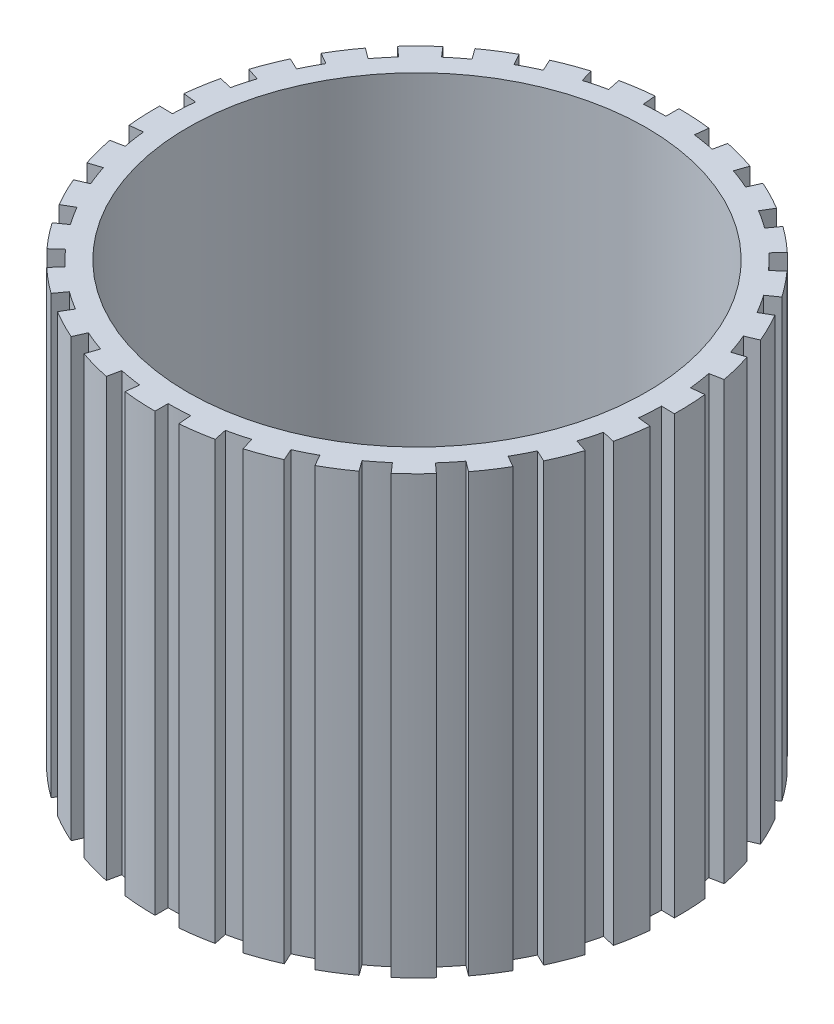
SolidWorks part; units mm, degrees
ref_plane "Front Plane" through (0, 0, 0) normal (0, 0, 1) x (1, 0, 0)
ref_plane "Top Plane" through (0, 0, 0) normal (0, 1, 0) x (1, 0, 0)
ref_plane "Right Plane" through (0, 0, 0) normal (1, 0, 0) x (0, 0, -1)
sketch "Sketch1" plane through (0, 0, 0) normal (0, 1, 0) x (1, 0, 0)
  line L0 (0, 57) -> (0, 60)
  line L1 (6.9466, 56.5751) -> (7.3122, 59.5528)
  line L2 (11.851, 55.7544) -> (12.4747, 58.6889)
  line L3 (18.5574, 53.8946) -> (19.5341, 56.7311)
  line L4 (23.184, 52.0721) -> (24.4042, 54.8127)
  line L5 (29.3572, 48.8585) -> (30.9023, 51.43)
  line L6 (33.5038, 46.114) -> (35.2671, 48.541)
  line L7 (38.8739, 41.6872) -> (40.9199, 43.8812)
  line L8 (42.3593, 38.1404) -> (44.5887, 40.1478)
  line L9 (46.6917, 32.6939) -> (49.1491, 34.4146)
  line L10 (49.3634, 28.5) -> (51.9615, 30)
  line L11 (52.4688, 22.2717) -> (55.2303, 23.4439)
  line L12 (54.2102, 17.614) -> (57.0634, 18.541)
  line L13 (55.9527, 10.8761) -> (58.8976, 11.4485)
  line L14 (56.6877, 5.9581) -> (59.6713, 6.2717)
  line L15 (56.9913, -0.9948) -> (59.9909, -1.0471)
  line L16 (56.6877, -5.9581) -> (59.6713, -6.2717)
  line L17 (55.5391, -12.8222) -> (58.4622, -13.4971)
  line L18 (54.2102, -17.614) -> (57.0634, -18.541)
  line L19 (51.6595, -24.0892) -> (54.3785, -25.3571)
  line L20 (49.3634, -28.5) -> (51.9615, -30)
  line L21 (45.5222, -34.3035) -> (47.9181, -36.1089)
  line L22 (42.3593, -38.1404) -> (44.5887, -40.1478)
  line L23 (37.3954, -43.0184) -> (39.3635, -45.2826)
  line L24 (33.5038, -46.114) -> (35.2671, -48.541)
  line L25 (27.6341, -49.8533) -> (29.0886, -52.4772)
  line L26 (23.184, -52.0721) -> (24.4042, -54.8127)
  line L27 (16.6652, -54.5094) -> (17.5423, -57.3783)
  line L28 (11.851, -55.7544) -> (12.4747, -58.6889)
  line L29 (4.9679, -56.7831) -> (5.2293, -59.7717)
  line L30 (0, -57) -> (0, -60)
  line L31 (-6.9466, -56.5751) -> (-7.3122, -59.5528)
  line L32 (-11.851, -55.7544) -> (-12.4747, -58.6889)
  line L33 (-18.5574, -53.8946) -> (-19.5341, -56.7311)
  line L34 (-23.184, -52.0721) -> (-24.4042, -54.8127)
  line L35 (-29.3572, -48.8585) -> (-30.9023, -51.43)
  line L36 (-33.5038, -46.114) -> (-35.2671, -48.541)
  line L37 (-38.8739, -41.6872) -> (-40.9199, -43.8812)
  line L38 (-42.3593, -38.1404) -> (-44.5887, -40.1478)
  line L39 (-46.6917, -32.6939) -> (-49.1491, -34.4146)
  line L40 (-49.3634, -28.5) -> (-51.9615, -30)
  line L41 (-52.4688, -22.2717) -> (-55.2303, -23.4439)
  line L42 (-54.2102, -17.614) -> (-57.0634, -18.541)
  line L43 (-55.9527, -10.8761) -> (-58.8976, -11.4485)
  line L44 (-56.6877, -5.9581) -> (-59.6713, -6.2717)
  line L45 (-56.9913, 0.9948) -> (-59.9909, 1.0471)
  line L46 (-56.6877, 5.9581) -> (-59.6713, 6.2717)
  line L47 (-55.5391, 12.8222) -> (-58.4622, 13.4971)
  line L48 (-54.2102, 17.614) -> (-57.0634, 18.541)
  line L49 (-51.6595, 24.0892) -> (-54.3785, 25.3571)
  line L50 (-49.3634, 28.5) -> (-51.9615, 30)
  line L51 (-45.5222, 34.3035) -> (-47.9181, 36.1089)
  line L52 (-42.3593, 38.1404) -> (-44.5887, 40.1478)
  line L53 (-37.3954, 43.0184) -> (-39.3635, 45.2826)
  line L54 (-33.5038, 46.114) -> (-35.2671, 48.541)
  line L55 (-27.6341, 49.8533) -> (-29.0886, 52.4772)
  line L56 (-23.184, 52.0721) -> (-24.4042, 54.8127)
  line L57 (-16.6652, 54.5094) -> (-17.5423, 57.3783)
  line L58 (-11.851, 55.7544) -> (-12.4747, 58.6889)
  line L59 (-4.9679, 56.7831) -> (-5.2293, 59.7717)
  circle A0 centre (0, 0) radius 52.5
  arc A1 (7.3122, 59.5528) -> (0, 60) centre (0, 0) ccw
  arc A2 (11.851, 55.7544) -> (6.9466, 56.5751) centre (0, 0) ccw
  arc A3 (19.5341, 56.7311) -> (12.4747, 58.6889) centre (0, 0) ccw
  arc A4 (23.184, 52.0721) -> (18.5574, 53.8946) centre (0, 0) ccw
  arc A5 (30.9023, 51.43) -> (24.4042, 54.8127) centre (0, 0) ccw
  arc A6 (33.5038, 46.114) -> (29.3572, 48.8585) centre (0, 0) ccw
  arc A7 (40.9199, 43.8812) -> (35.2671, 48.541) centre (0, 0) ccw
  arc A8 (42.3593, 38.1404) -> (38.8739, 41.6872) centre (0, 0) ccw
  arc A9 (49.1491, 34.4146) -> (44.5887, 40.1478) centre (0, 0) ccw
  arc A10 (49.3634, 28.5) -> (46.6917, 32.6939) centre (0, 0) ccw
  arc A11 (55.2303, 23.4439) -> (51.9615, 30) centre (0, 0) ccw
  arc A12 (54.2102, 17.614) -> (52.4688, 22.2717) centre (0, 0) ccw
  arc A13 (58.8976, 11.4485) -> (57.0634, 18.541) centre (0, 0) ccw
  arc A14 (56.6877, 5.9581) -> (55.9527, 10.8761) centre (0, 0) ccw
  arc A15 (59.9909, -1.0471) -> (59.6713, 6.2717) centre (0, 0) ccw
  arc A16 (56.6877, -5.9581) -> (56.9913, -0.9948) centre (0, 0) ccw
  arc A17 (58.4622, -13.4971) -> (59.6713, -6.2717) centre (0, 0) ccw
  arc A18 (54.2102, -17.614) -> (55.5391, -12.8222) centre (0, 0) ccw
  arc A19 (54.3785, -25.3571) -> (57.0634, -18.541) centre (0, 0) ccw
  arc A20 (49.3634, -28.5) -> (51.6595, -24.0892) centre (0, 0) ccw
  arc A21 (47.9181, -36.1089) -> (51.9615, -30) centre (0, 0) ccw
  arc A22 (42.3593, -38.1404) -> (45.5222, -34.3035) centre (0, 0) ccw
  arc A23 (39.3635, -45.2826) -> (44.5887, -40.1478) centre (0, 0) ccw
  arc A24 (33.5038, -46.114) -> (37.3954, -43.0184) centre (0, 0) ccw
  arc A25 (29.0886, -52.4772) -> (35.2671, -48.541) centre (0, 0) ccw
  arc A26 (23.184, -52.0721) -> (27.6341, -49.8533) centre (0, 0) ccw
  arc A27 (17.5423, -57.3783) -> (24.4042, -54.8127) centre (0, 0) ccw
  arc A28 (11.851, -55.7544) -> (16.6652, -54.5094) centre (0, 0) ccw
  arc A29 (5.2293, -59.7717) -> (12.4747, -58.6889) centre (0, 0) ccw
  arc A30 (0, -57) -> (4.9679, -56.7831) centre (0, 0) ccw
  arc A31 (-7.3122, -59.5528) -> (0, -60) centre (0, 0) ccw
  arc A32 (-11.851, -55.7544) -> (-6.9466, -56.5751) centre (0, 0) ccw
  arc A33 (-19.5341, -56.7311) -> (-12.4747, -58.6889) centre (0, 0) ccw
  arc A34 (-23.184, -52.0721) -> (-18.5574, -53.8946) centre (0, 0) ccw
  arc A35 (-30.9023, -51.43) -> (-24.4042, -54.8127) centre (0, 0) ccw
  arc A36 (-33.5038, -46.114) -> (-29.3572, -48.8585) centre (0, 0) ccw
  arc A37 (-40.9199, -43.8812) -> (-35.2671, -48.541) centre (0, 0) ccw
  arc A38 (-42.3593, -38.1404) -> (-38.8739, -41.6872) centre (0, 0) ccw
  arc A39 (-49.1491, -34.4146) -> (-44.5887, -40.1478) centre (0, 0) ccw
  arc A40 (-49.3634, -28.5) -> (-46.6917, -32.6939) centre (0, 0) ccw
  arc A41 (-55.2303, -23.4439) -> (-51.9615, -30) centre (0, 0) ccw
  arc A42 (-54.2102, -17.614) -> (-52.4688, -22.2717) centre (0, 0) ccw
  arc A43 (-58.8976, -11.4485) -> (-57.0634, -18.541) centre (0, 0) ccw
  arc A44 (-56.6877, -5.9581) -> (-55.9527, -10.8761) centre (0, 0) ccw
  arc A45 (-59.9909, 1.0471) -> (-59.6713, -6.2717) centre (0, 0) ccw
  arc A46 (-56.6877, 5.9581) -> (-56.9913, 0.9948) centre (0, 0) ccw
  arc A47 (-58.4622, 13.4971) -> (-59.6713, 6.2717) centre (0, 0) ccw
  arc A48 (-54.2102, 17.614) -> (-55.5391, 12.8222) centre (0, 0) ccw
  arc A49 (-54.3785, 25.3571) -> (-57.0634, 18.541) centre (0, 0) ccw
  arc A50 (-49.3634, 28.5) -> (-51.6595, 24.0892) centre (0, 0) ccw
  arc A51 (-47.9181, 36.1089) -> (-51.9615, 30) centre (0, 0) ccw
  arc A52 (-42.3593, 38.1404) -> (-45.5222, 34.3035) centre (0, 0) ccw
  arc A53 (-39.3635, 45.2826) -> (-44.5887, 40.1478) centre (0, 0) ccw
  arc A54 (-33.5038, 46.114) -> (-37.3954, 43.0184) centre (0, 0) ccw
  arc A55 (-29.0886, 52.4772) -> (-35.2671, 48.541) centre (0, 0) ccw
  arc A56 (-23.184, 52.0721) -> (-27.6341, 49.8533) centre (0, 0) ccw
  arc A57 (-17.5423, 57.3783) -> (-24.4042, 54.8127) centre (0, 0) ccw
  arc A58 (-11.851, 55.7544) -> (-16.6652, 54.5094) centre (0, 0) ccw
  arc A59 (-5.2293, 59.7717) -> (-12.4747, 58.6889) centre (0, 0) ccw
  arc A60 (0, 57) -> (-4.9679, 56.7831) centre (0, 0) ccw
  point P156 (0, 0)
  dimension "D1" = 105
  dimension "D2" = 120
  dimension "D3" = 114
  dimension "D4" = 7
  dimension "D5" = 7
  dimension "D6" = 5
  dimension "D7" = 57
  dimension "D8" = 30
extrude "Boss-Extrude1" add sketch "Sketch1" along normal blind 100 contours L0 A60 L59 A59 L58 A58 L57 A57 L56 A56 L55 A55 L54 A54 L53 A53 L52 A52 L51 A51 L50 A50 L49 A49 L48 A48 L47 A47 L46 A46 L45 A45 L44 A44 L43 A43 L42 A42 L41 A41 L40 A40 L39 A39 L38 A38 L37 A37 L36 A36 L35
